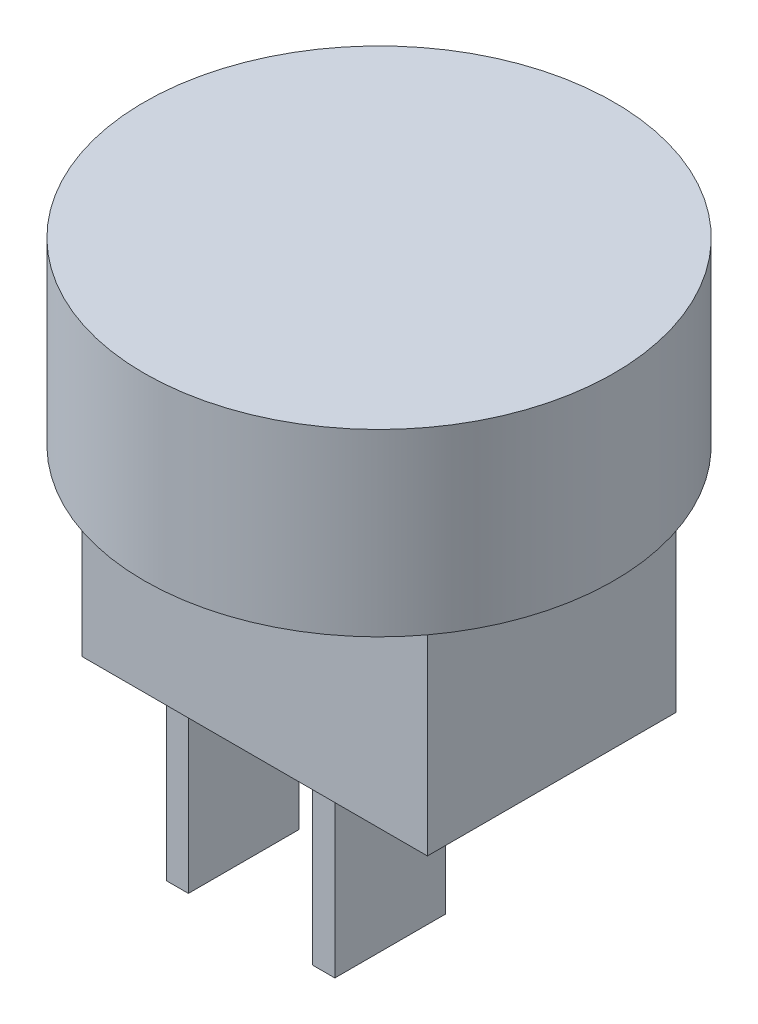
SolidWorks part; units mm, degrees
ref_plane "Přední rovina" through (0, 0, 0) normal (0, 0, 1) x (1, 0, 0)
ref_plane "Horní rovina" through (0, 0, 0) normal (0, 1, 0) x (1, 0, 0)
ref_plane "Pravá rovina" through (0, 0, 0) normal (1, 0, 0) x (0, 0, -1)
sketch "Skica2" plane through (0, 0, 0) normal (0, 1, 0) x (1, 0, 0)
  line L1 (-6.25, 4.5) -> (6.25, 4.5)
  line L2 (-6.25, 4.5) -> (-6.25, -4.5)
  line L3 (-6.25, -4.5) -> (6.25, -4.5)
  line L4 (6.25, 4.5) -> (6.25, -4.5)
  line L5 (-6.25, 4.5) -> (6.25, -4.5) construction
  line L6 (-6.25, -4.5) -> (6.25, 4.5) construction
  point P0 (0, 0)
  dimension "D1" = 9
  dimension "D2" = 12.5
extrude "Přidat vysunutím1" add sketch "Skica2" along normal blind 7.5
sketch "Skica3" plane through (0, 7.5, 0) normal (0, 1, 0) x (1, 0, 0)
  circle A0 centre (0, 0) radius 8.5
  dimension "D1" = 17
extrude "Přidat vysunutím2" add sketch "Skica3" along normal blind 6.5
sketch "Skica4" plane through (0, 0, 0) normal (0, -1, 0) x (-1, 0, 0)
  line L0 (10.9592, 0) -> (-13.0371, 0) construction
  line L1 (5.7, -2) -> (4.9, -2)
  line L2 (0.4, -2) -> (-0.4, -2)
  line L3 (0.4, -2) -> (0.4, 2)
  line L4 (0.4, 2) -> (-0.4, 2)
  line L5 (-0.4, -2) -> (-0.4, 2)
  line L6 (0.4, -2) -> (-0.4, 2) construction
  line L7 (0.4, 2) -> (-0.4, -2) construction
  line L8 (5.7, -2) -> (5.7, 2)
  line L9 (5.7, 2) -> (4.9, 2)
  line L10 (4.9, -2) -> (4.9, 2)
  line L11 (5.7, -2) -> (4.9, 2) construction
  line L12 (5.7, 2) -> (4.9, -2) construction
  point P3 (0, 0)
  point P8 (5.3, 0)
  point P13 (0, 0)
  dimension "D1" = 0.8
  dimension "D2" = 4
  dimension "D3" = 4.5
  dimension "D4" = 0.8
  dimension "D5" = 4
extrude "Přidat vysunutím3" add sketch "Skica4" along normal blind 8
